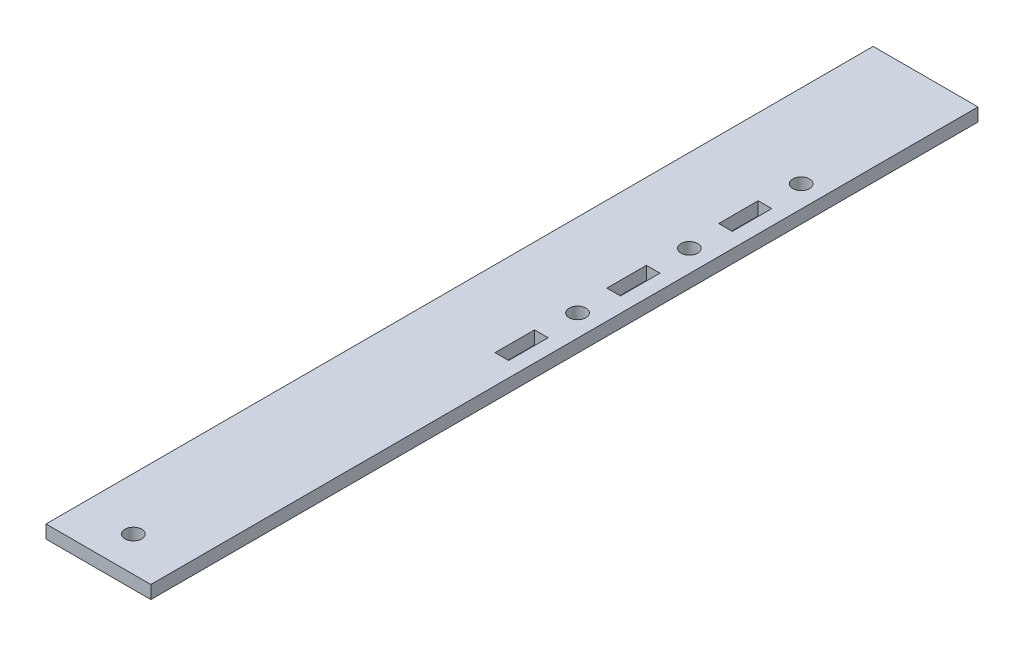
SolidWorks part; units mm, degrees
ref_plane "Front Plane" through (0, 0, 0) normal (0, 0, 1) x (1, 0, 0)
ref_plane "Top Plane" through (0, 0, 0) normal (0, 1, 0) x (1, 0, 0)
ref_plane "Right Plane" through (0, 0, 0) normal (1, 0, 0) x (0, 0, -1)
sketch "Sketch1" plane through (0, 0, 0) normal (0, 0, 1) x (1, 0, 0)
  line L0 (0, 0) -> (0, 2.3813)
  line L1 (0, 2.3813) -> (19.05, 2.3813)
  line L2 (19.05, 2.3813) -> (19.05, 0)
  line L3 (19.05, 0) -> (0, 0)
  dimension "D1" = 2.3813
  dimension "D2" = 19.05
extrude "Boss-Extrude1" add sketch "Sketch1" along normal blind 88.9
sketch "Sketch5" plane through (0, 2.3813, 0) normal (0, 1, 0) x (1, 0, 0)
  line L0 (16.6687, -25.4) -> (19.05, -25.4)
  line L2 (19.05, -88.9) -> (19.05, 0) construction
  line L10 (15.0813, -39.1478) -> (15.0813, -49.3078)
  line L11 (15.0813, -49.3078) -> (15.0813, -45.72)
  line L17 (15.0813, -49.3078) -> (15.0813, -52.8955)
  line L24 (16.3176, -28.9877) -> (16.3176, -32.5755)
  line L25 (15.0813, -52.8955) -> (16.3176, -52.8955)
  line L26 (15.0813, -52.8955) -> (13.8449, -52.8955)
  line L27 (13.8449, -52.8955) -> (13.8449, -45.72)
  line L28 (13.8449, -45.72) -> (16.3176, -45.72)
  line L29 (16.3176, -45.72) -> (16.3176, -52.8955)
  line L30 (16.3176, -32.5755) -> (15.0813, -32.5755)
  line L31 (15.0813, -32.5755) -> (13.8449, -32.5755)
  line L32 (13.8449, -32.5755) -> (13.8449, -25.4)
  line L33 (13.8449, -25.4) -> (16.3176, -25.4)
  line L34 (16.3176, -25.4) -> (16.3176, -28.9877)
  circle A0 centre (15.0813, -39.1478) radius 1.524
  circle A3 centre (15.0813, -18.8277) radius 1.524
  dimension "D7" = 10.16
  dimension "D10" = 7.1755
  dimension "D2" = 2.3813
  dimension "D3" = 3.5877
  dimension "D4" = 1.2363
  dimension "D5" = 1.2363
  dimension "D8" = 3.5878
  dimension "D9" = 1.2363
sketch "Sketch6" plane through (0, 2.3813, 0) normal (0, 1, 0) x (1, 0, 0)
sketch "Sketch7" plane through (0, 2.3813, 0) normal (0, 1, 0) x (1, 0, 0)
extrude "Cut-Extrude4" cut sketch "Sketch5" against normal through all
sketch "Sketch8" plane through (0, 2.3813, 0) normal (0, 1, 0) x (1, 0, 0)
  line L0 (0, -88.9) -> (0, -114.3)
  line L2 (19.05, -114.3) -> (19.05, -88.9)
  line L3 (0, -88.9) -> (19.05, -88.9)
  line L4 (0, -114.3) -> (0, -120.65)
  line L5 (0, -120.65) -> (19.05, -120.65)
  line L6 (19.05, -120.65) -> (19.05, -114.3)
  dimension "D1" = 25.4
  dimension "D2" = 6.35
sketch "Sketch9" plane through (0, 2.3813, 0) normal (0, 1, 0) x (1, 0, 0)
  line L0 (0, 0) -> (0, 29.6545)
  line L1 (0, 29.6545) -> (19.05, 29.6545)
  line L2 (19.05, 29.6545) -> (19.05, 0)
  line L3 (0, 0) -> (19.05, 0)
  dimension "D1" = 29.6545
extrude "Boss-Extrude4" add sketch "Sketch9" against normal blind 2.3813
sketch "Sketch10" plane through (0, 2.3813, 0) normal (0, 1, 0) x (1, 0, 0)
  line L0 (13.5572, -18.8277) -> (16.6053, -18.8277)
  line L1 (13.8449, -8.6677) -> (16.3176, -8.6677)
  line L4 (16.3176, -8.6677) -> (16.3176, -5.08)
  line L5 (16.3176, -5.08) -> (13.8449, -5.08)
  line L6 (13.8449, -5.08) -> (13.8449, -8.6677)
  line L7 (13.8449, -8.6677) -> (13.8449, -12.2555)
  line L8 (13.8449, -12.2555) -> (16.3176, -12.2555)
  line L9 (16.3176, -12.2555) -> (16.3176, -8.6677)
  circle A0 centre (15.0813, -18.8277) radius 1.524 construction
  circle A1 centre (15.0813, 1.4923) radius 1.524
  dimension "D1" = 2.4727
  dimension "D2" = 3.5877
  dimension "D3" = 3.5877
extrude "Cut-Extrude5" cut sketch "Sketch10" against normal through all contours L5 L6 L1 L4 | L8 L9 L1 L7 | A1
extrude "Boss-Extrude5" add sketch "Sketch8" against normal blind 2.3813
sketch "Sketch11" plane through (0, 2.3813, 0) normal (0, 1, 0) x (1, 0, 0)
  circle A0 centre (9.525, -114.3) radius 1.524
  dimension "D2" = 3.048
extrude "Cut-Extrude6" cut sketch "Sketch11" against normal through all
